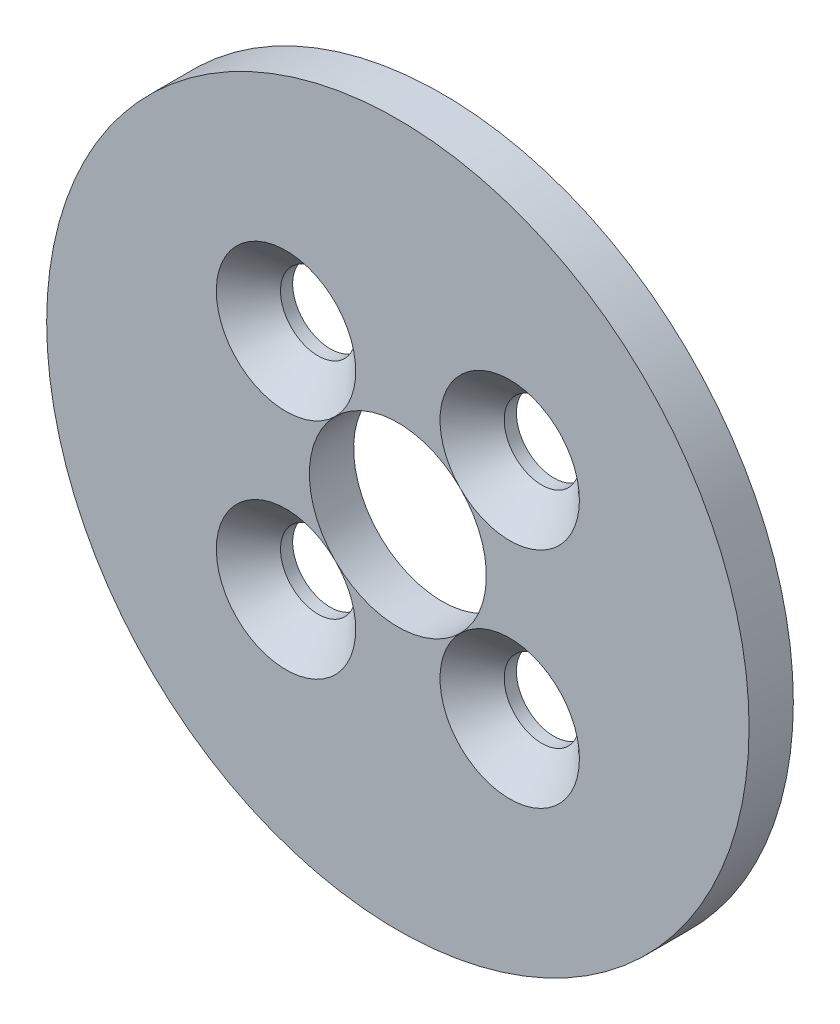
SolidWorks part; units mm, degrees
ref_plane "Front Plane" through (0, 0, 0) normal (0, 0, 1) x (1, 0, 0)
ref_plane "Top Plane" through (0, 0, 0) normal (0, 1, 0) x (1, 0, 0)
ref_plane "Right Plane" through (0, 0, 0) normal (1, 0, 0) x (0, 0, -1)
sketch "Sketch2" plane through (0, 0, 0) normal (0, 0, 1) x (1, 0, 0)
  circle A0 centre (-160.6068, 98.8856) radius 15.875
  circle A1 centre (-165.6626, 103.9414) radius 1.7
  circle A2 centre (-155.5509, 103.9414) radius 1.7
  circle A3 centre (-155.5509, 93.8298) radius 1.7
  circle A4 centre (-165.6626, 93.8298) radius 1.7
  circle A5 centre (-160.6068, 98.8856) radius 4
  circle A6 centre (-160.6068, 98.8856) radius 7.15 construction
  point P15 (-160.7128, 98.9917)
  point P16 (-160.6068, 98.8856)
  dimension "D1" = 3.4
  dimension "D2" = 4
  dimension "D4" = 31.75
  dimension "D5" = 14.3
extrude "Boss-Extrude1" add sketch "Sketch2" along normal blind 2
hole_wizard "CSK for M3 Flat Head Machine Screw2" positions "3DSketch2" profile "Sketch4" countersink size "M3" standard "ANSI Metric" end condition through all
sketch3d "3DSketch2"
  line L0 (-165.6626, 103.9414, 2) -> (-165.6626, 103.9414, 0) construction
  line L1 (-155.5509, 103.9414, 2) -> (-155.5509, 103.9414, 0) construction
  line L2 (-155.5509, 93.8298, 2) -> (-155.5509, 93.8298, 0) construction
  line L3 (-165.6626, 93.8298, 2) -> (-165.6626, 93.8298, 0) construction
  point P0 (-165.6626, 103.9414, 2)
  point P4 (-155.5509, 103.9414, 2)
  point P8 (-155.5509, 93.8298, 2)
  point P12 (-165.6626, 93.8298, 2)
sketch "Sketch4" plane through (-165.6626, 103.9414, 2) normal (1, 0, 0) x (0, -1, 0)
  line L0 (0, 0) -> (0, 2)
  line L1 (0, 2) -> (1.7, 2)
  line L2 (1.7, 2) -> (1.7, 1.45)
  line L3 (1.7, 1.45) -> (3.15, 0)
  line L5 (3.15, 0) -> (0, 0)
  line L6 (-1.7, 1.45) -> (-3.15, 0) construction
  line L11 (0, -6.35) -> (0, 107.95) construction
  dimension "Thru Hole Dia." = 3.4
  dimension "Thru Hole Depth" = 2
  dimension "Near C'Sink Dia." = 6.3
  dimension "Near C'Sink Angle" = 90
